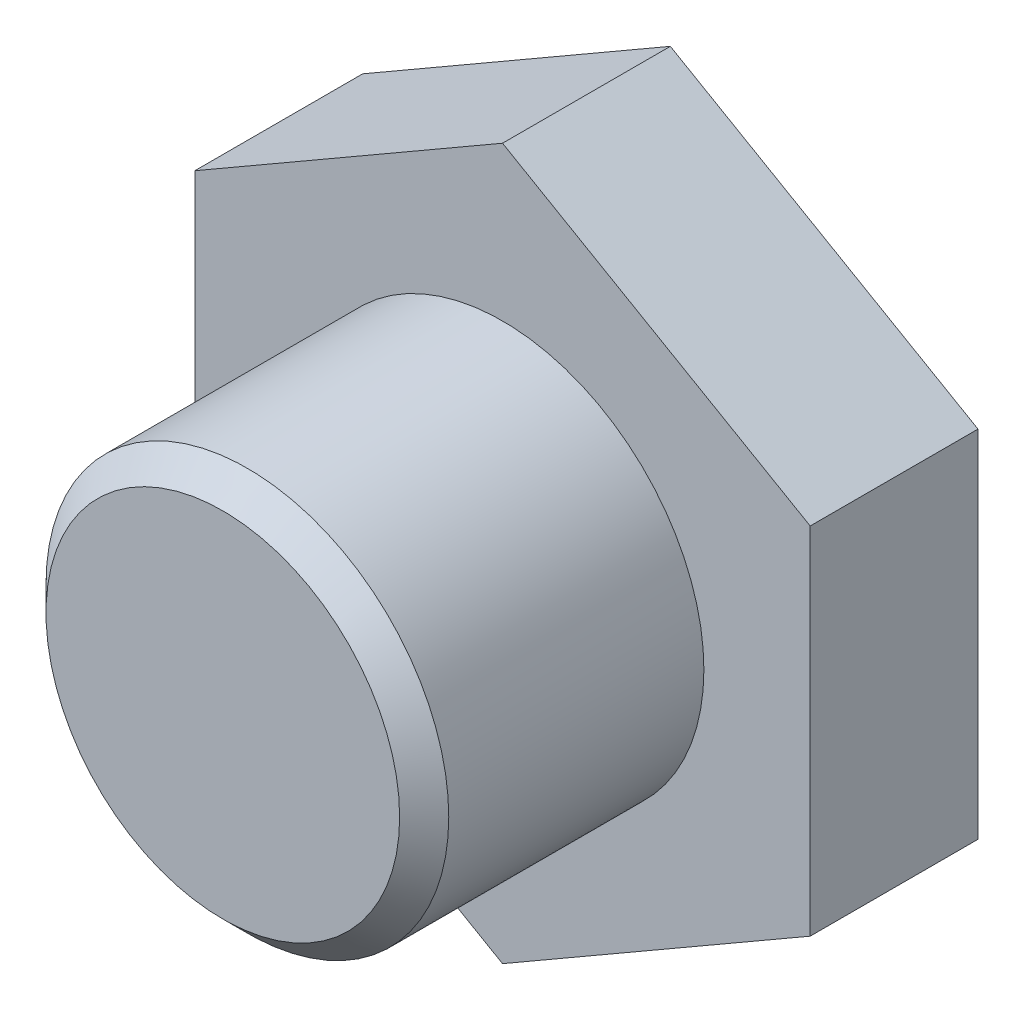
SolidWorks part; units mm, degrees
material "Сталь"
ref_plane "Спереди" through (0, 0, 0) normal (0, 0, 1) x (1, 0, 0)
ref_plane "Сверху" through (0, 0, 0) normal (0, 1, 0) x (1, 0, 0)
ref_plane "Справа" through (0, 0, 0) normal (1, 0, 0) x (0, 0, -1)
sketch "Эскиз1" plane through (0, 0, 0) normal (0, 0, 1) x (1, 0, 0)
  line L1 (0, 31.7543) -> (-27.5, 15.8771)
  line L2 (-27.5, 15.8771) -> (-27.5, -15.8771)
  line L3 (-27.5, -15.8771) -> (0, -31.7543)
  line L4 (0, -31.7543) -> (27.5, -15.8771)
  line L5 (27.5, -15.8771) -> (27.5, 15.8771)
  line L6 (27.5, 15.8771) -> (0, 31.7543)
  circle A0 centre (0, 0) radius 27.5 construction
  dimension "D1" = 55
extrude "Бобышка-Вытянуть1" add sketch "Эскиз1" along normal blind 15
sketch "Эскиз2" plane through (0, 0, 15) normal (0, 0, 1) x (1, 0, 0)
  circle A0 centre (0, 0) radius 18
  dimension "D1" = 36
extrude "Бобышка-Вытянуть2" add sketch "Эскиз2" along normal blind 25
cosmetic thread "Условное изображение резьбы1" parameters "D2"=31.61
chamfer "Фаска1" distance 2.195 angle 45 1 edges at (18, 0, 40)
